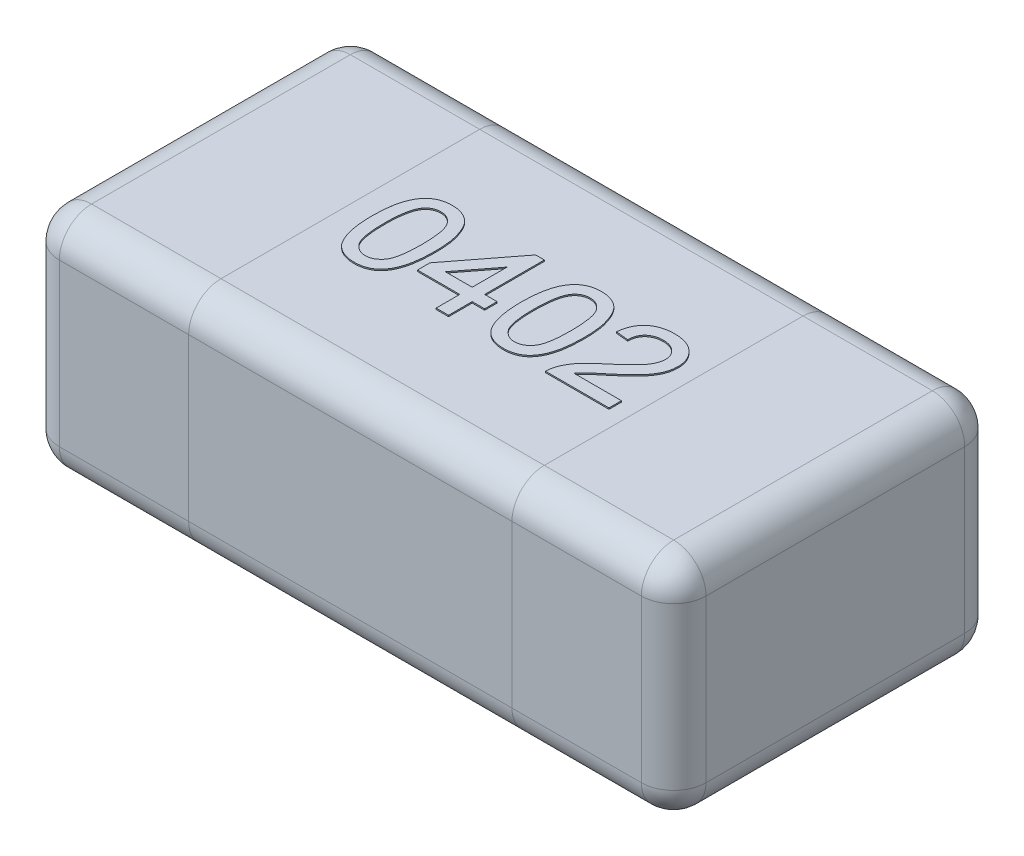
SolidWorks part; units mm, degrees
ref_plane "Front" through (0, 0, 0) normal (0, 0, 1) x (1, 0, 0)
ref_plane "Top" through (0, 0, 0) normal (0, 1, 0) x (1, 0, 0)
ref_plane "Right" through (0, 0, 0) normal (1, 0, 0) x (0, 0, -1)
sketch "Sketch1" plane through (0, 0, 0) normal (0, 1, 0) x (1, 0, 0)
  line L0 (0, -5.3126) -> (0, 5.729) construction
  line L1 (-6.1479, 0) -> (7.7291, 0) construction
  line L3 (-0.5, 0.25) -> (0.5, 0.25)
  line L4 (-0.5, 0.25) -> (-0.5, -0.25)
  line L5 (-0.5, -0.25) -> (0.5, -0.25)
  line L6 (0.5, 0.25) -> (0.5, -0.25)
  dimension "D1" = 1
  dimension "D2" = 0.5
extrude "Extrude1" add sketch "Sketch1" along normal blind 0.35
fillet "Fillet1" radius 0.05 12 edges at (0, 0.35, 0.25) (-0.5, 0.175, -0.25) (0, 0, -0.25) (-0.5, 0, 0) (-0.5, 0.175, 0.25) (0, 0, 0.25) (0.5, 0.175, 0.25) (0.5, 0.175, -0.25) (0.5, 0, 0) (0, 0.35, -0.25) (0.5, 0.35, 0) (-0.5, 0.35, 0)
sketch "Sketch2" plane through (0, 0, 0.25) normal (0, 0, 1) x (1, 0, 0)
  line L0 (-0.45, 0.35) -> (0.45, 0.35) construction
  line L1 (-0.25, 0.35) -> (0.25, 0.35)
  line L2 (-0.25, 0.35) -> (-0.25, 0)
  line L3 (-0.25, 0) -> (0.25, 0)
  line L4 (0.25, 0.35) -> (0.25, 0)
  line L5 (0.45, 0) -> (-0.45, 0) construction
  line L6 (-0.5, 0.05) -> (-0.5, 0.3) construction
  line L7 (0, -0.2963) -> (0, 3.0124) construction
  dimension "D1" = 0.25
split line "Split Line1"
sketch "Sketch3" plane through (0, 0.35, 0) normal (0, 1, 0) x (1, 0, 0)
  text T0 "0402" font "Arial" height 0.15
  dimension "D1" = 0.225
  dimension "D2" = 0.075
extrude "Extrude2" add sketch "Sketch3" along normal blind 0.002
